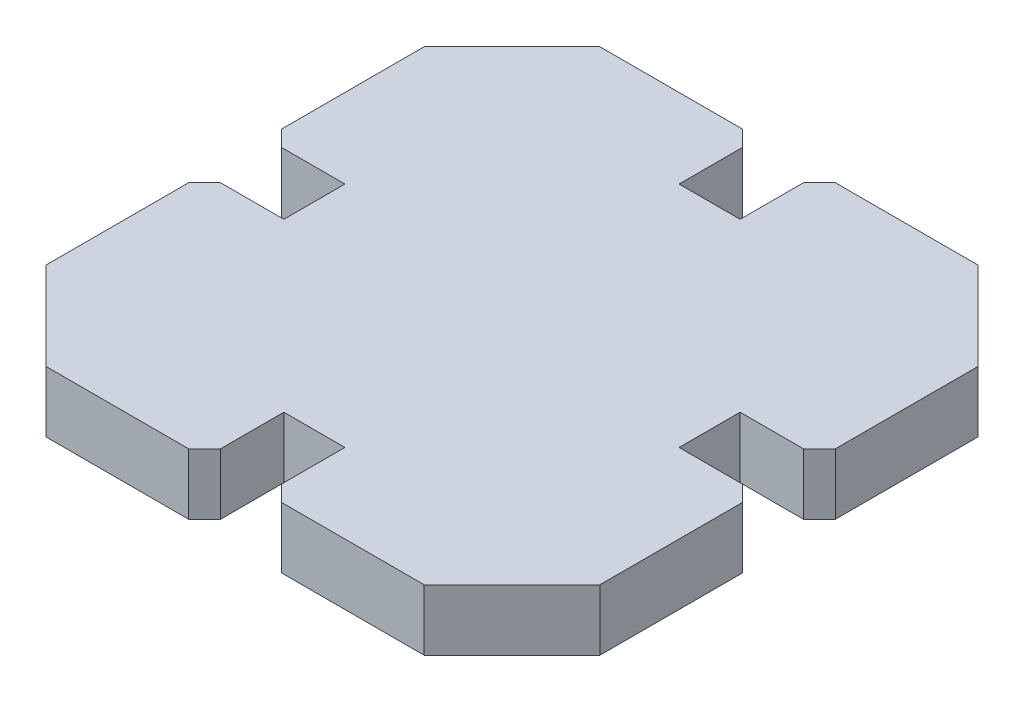
SolidWorks part; units mm, degrees
ref_plane "Front" through (0, 0, 0) normal (0, 0, 1) x (1, 0, 0)
ref_plane "Top" through (0, 0, 0) normal (0, 1, 0) x (1, 0, 0)
ref_plane "Right" through (0, 0, 0) normal (1, 0, 0) x (0, 0, -1)
sketch "Sketch1" plane through (0, 0, 0) normal (0, 1, 0) x (1, 0, 0)
  line L0 (17.4608, -11.925) -> (11.925, -17.4608)
  line L1 (17.4608, -1.925) -> (17.4608, -11.925)
  line L2 (17.4608, 1.925) -> (17.4608, 11.925)
  line L3 (-11.925, 17.4608) -> (11.925, 17.4608) construction
  line L4 (17.4608, 1.925) -> (12.4608, 1.925)
  line L5 (0, 0) -> (-31.6842, 0) construction
  line L6 (0, 0) -> (0, -0.7623) construction
  line L7 (-1.925, 17.4608) -> (-11.925, 17.4608)
  line L8 (-1.925, 17.4608) -> (-1.925, 12.4608)
  line L9 (-1.925, 12.4608) -> (1.925, 12.4608)
  line L10 (1.925, 17.4608) -> (1.925, 12.4608)
  line L11 (1.925, 17.4608) -> (11.925, 17.4608)
  line L12 (12.4608, 1.925) -> (12.4608, -1.925)
  line L13 (17.4608, -1.925) -> (12.4608, -1.925)
  line L14 (-11.925, -17.4608) -> (-17.4608, -11.925)
  line L15 (-1.925, -17.4608) -> (-11.925, -17.4608)
  line L16 (1.925, -17.4608) -> (11.925, -17.4608)
  line L17 (1.925, -17.4608) -> (1.925, -12.4608)
  line L18 (1.925, -12.4608) -> (-1.925, -12.4608)
  line L19 (-1.925, -17.4608) -> (-1.925, -12.4608)
  line L20 (-17.4608, 11.925) -> (-11.925, 17.4608)
  line L21 (-17.4608, 1.925) -> (-17.4608, 11.925)
  line L22 (-17.4608, -1.925) -> (-17.4608, -11.925)
  line L23 (-17.4608, -1.925) -> (-12.4608, -1.925)
  line L24 (-12.4608, -1.925) -> (-12.4608, 1.925)
  line L25 (-17.4608, 1.925) -> (-12.4608, 1.925)
  line L26 (0, -0.7623) -> (0, -24.8863) construction
  line L27 (0, 0) -> (0, 19.2169) construction
  line L28 (11.925, 17.4608) -> (17.4608, 11.925)
  line L31 (-0.1098, 0) -> (28.3163, 0) construction
  point P0 (0, 0)
  point P33 (-0.1508, 0.1408)
  point P40 (0, 0)
  dimension "D2" = 3.85
  dimension "D3" = 5
  dimension "D5" = 45
  dimension "D1" = 10
  dimension "D6" = 10
  dimension "D4" = 17.4608
  dimension "D8" = 7.8287
  dimension "D7" = 4
extrude "Boss-Extrude1" add sketch "Sketch1" along normal blind 3.85
chamfer "Chamfer1" distance 1 angle 45 8 edges at (-1.925, 1.925, -17.4608) (1.925, 1.925, -17.4608) (17.4608, 1.925, 1.925) (17.4608, 1.925, -1.925) (1.925, 1.925, 17.4608) (-1.925, 1.925, 17.4608) (-17.4608, 1.925, 1.925) (-17.4608, 1.925, -1.925)
equation "\"entrance\"=5"
equation "\"D2@Sketch1\" = \"thick\""
equation "\"D3@Sketch1\"=\"entrance\""
equation "\"D1@Boss-Extrude1\"= \"thick\""
equation "\"thick\"=3.85"
